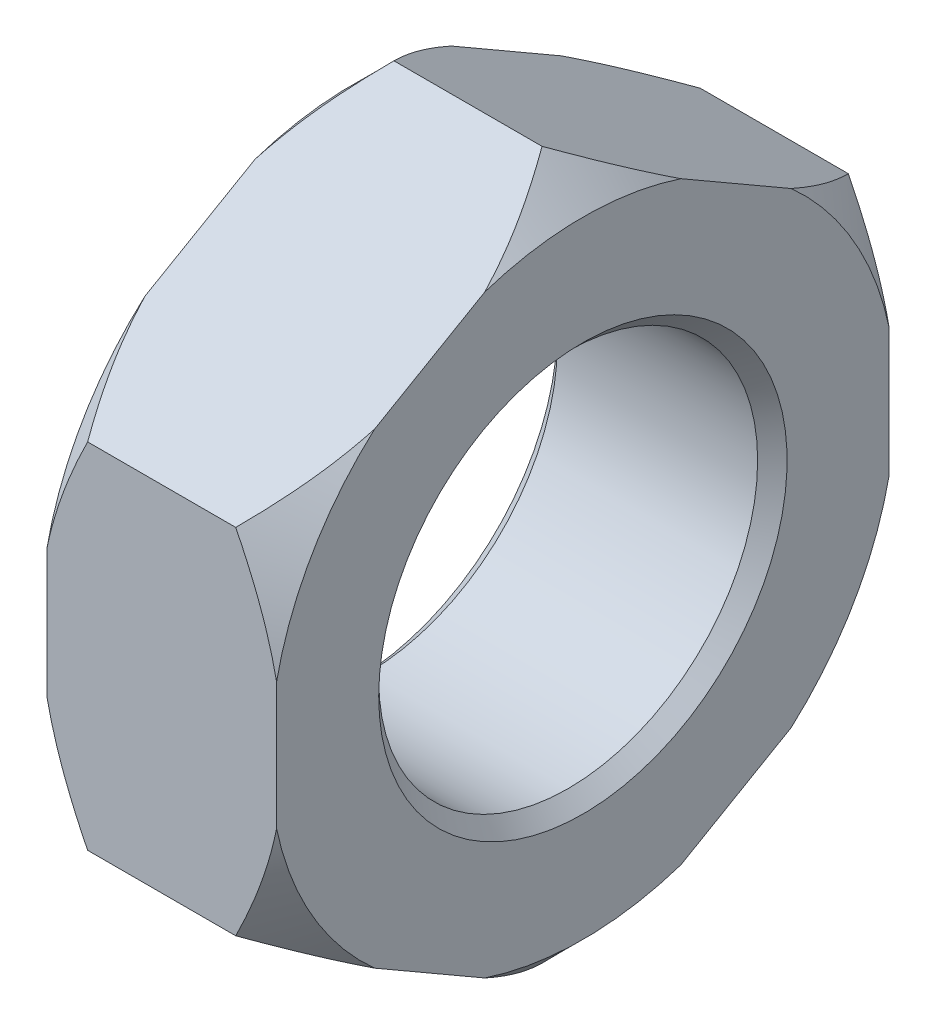
SolidWorks part; units mm, degrees
ref_plane "Plano frontal" through (0, 0, 0) normal (0, 0, 1) x (1, 0, 0)
ref_plane "Plano superior" through (0, 0, 0) normal (0, 1, 0) x (1, 0, 0)
ref_plane "Plano direito" through (0, 0, 0) normal (1, 0, 0) x (0, 0, -1)
ref_plane "Plano1" through (0, 0, 0) normal (0, 0, 1) x (1, 0, 0)
sketch "Esboço1" plane through (0, 0, 0) normal (0, 0, 1) x (1, 0, 0)
  line L0 (0, 0) -> (0, 14.5923)
  line L1 (0, 14.5923) -> (3.175, 17.7673)
  line L2 (3.175, 17.7673) -> (7.5438, 17.7673)
  line L3 (7.5438, 17.7673) -> (10.7188, 14.5923)
  line L4 (10.7188, 14.5923) -> (10.7188, 0)
  line L5 (10.7188, 0) -> (0, 0)
  line L6 (10.7188, 0) -> (0, 0) construction
revolve "Revolução1" add sketch "Esboço1" angle 360 about L6
ref_plane "Plano2" through (0, 0, 0) normal (1, 0, 0) x (0, 0, -1)
sketch "Esboço2" plane through (0, 0, 0) normal (1, 0, 0) x (0, 0, -1)
  line L0 (-14.2875, -8.2489) -> (0, -16.4978)
  line L1 (0, -16.4978) -> (14.2875, -8.2489)
  line L2 (14.2875, -8.2489) -> (14.2875, 8.2489)
  line L3 (14.2875, 8.2489) -> (0, 16.4978)
  line L4 (0, 16.4978) -> (-14.2875, 8.2489)
  line L5 (-14.2875, 8.2489) -> (-14.2875, -8.2489)
  circle A0 centre (0, 0) radius 28.575
extrude "Corte-extrusão1" cut sketch "Esboço2" along normal blind 10.7188
ref_plane "Plano3" through (0, 0, 0) normal (0, 0, 1) x (1, 0, 0)
sketch "Esboço3" plane through (0, 0, 0) normal (0, 0, 1) x (1, 0, 0)
  line L0 (0, 0) -> (0, 9.525)
  line L1 (0, 9.525) -> (0.6871, 8.8379)
  line L2 (0.6871, 8.8379) -> (10.0317, 8.8379)
  line L3 (10.0317, 8.8379) -> (10.7188, 9.525)
  line L4 (10.7188, 9.525) -> (10.7188, 0)
  line L5 (10.7188, 0) -> (0, 0)
  line L6 (10.7188, 0) -> (0, 0) construction
revolve "Corte-Revolução1" cut sketch "Esboço3" angle 360 about L6
